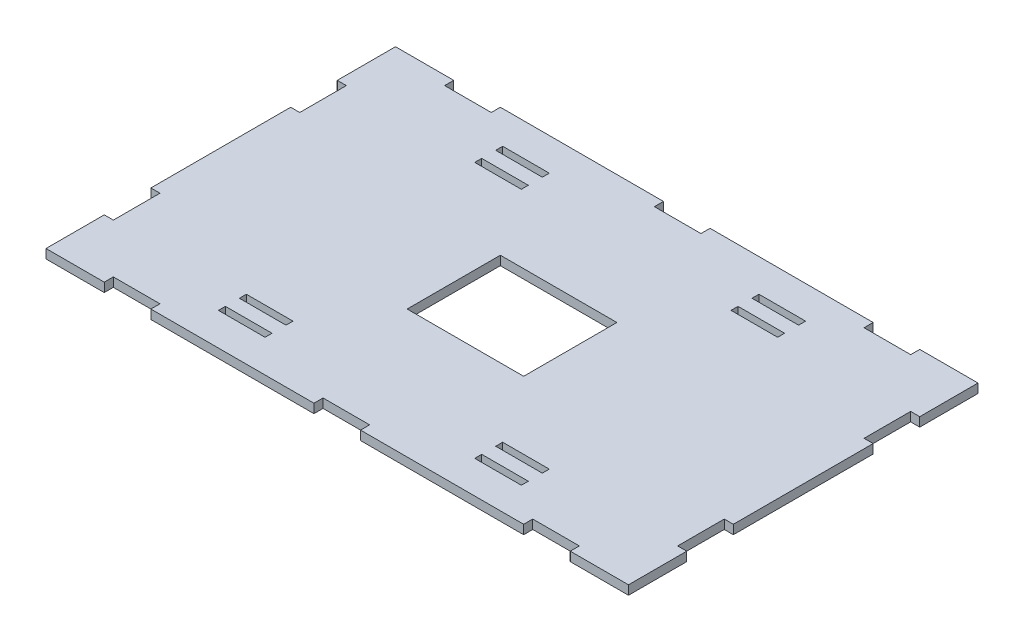
SolidWorks part; units mm, degrees
material "Very Low Density PE (SS)"
ref_plane "Front Plane" through (0, 0, 0) normal (0, 0, 1) x (1, 0, 0)
ref_plane "Top Plane" through (0, 0, 0) normal (0, 1, 0) x (1, 0, 0)
ref_plane "Right Plane" through (0, 0, 0) normal (1, 0, 0) x (0, 0, -1)
sketch "Sketch1" plane through (0, 0, 0) normal (0, 1, 0) x (1, 0, 0)
  line L0 (-125, 0) -> (125, 0) construction
  line L1 (-125, 75) -> (-100, 75)
  line L2 (-125, 75) -> (-125, 50)
  line L3 (-125, -75) -> (-100, -75)
  line L4 (125, 75) -> (125, 50)
  line L5 (0, 75) -> (0, -75) construction
  line L6 (-125, -55) -> (125, -55) construction
  line L11 (-65, -49) -> (-45, -49)
  line L12 (-65, -58) -> (-45, -58)
  line L25 (-65, -58) -> (-65, -61)
  line L26 (-25, 20) -> (25, 20)
  line L27 (-25, 20) -> (-25, -20)
  line L28 (-25, -20) -> (25, -20)
  line L29 (25, 20) -> (25, -20)
  line L30 (-25, 20) -> (25, -20) construction
  line L31 (-25, -20) -> (25, 20) construction
  line L32 (-65, -61) -> (-45, -61)
  line L33 (-45, -58) -> (-45, -61)
  line L34 (-45, -52) -> (-45, -49)
  line L35 (-65, -52) -> (-45, -52)
  line L36 (-65, -52) -> (-65, -49)
  line L37 (65, -61) -> (45, -61)
  line L38 (45, -58) -> (45, -61)
  line L39 (65, -58) -> (45, -58)
  line L40 (65, -58) -> (65, -61)
  line L41 (65, -52) -> (65, -49)
  line L42 (65, -52) -> (45, -52)
  line L43 (45, -52) -> (45, -49)
  line L44 (65, -49) -> (45, -49)
  line L45 (65, 52) -> (45, 52)
  line L46 (45, 52) -> (45, 49)
  line L47 (65, 49) -> (45, 49)
  line L48 (65, 52) -> (65, 49)
  line L49 (65, 58) -> (65, 61)
  line L50 (65, 58) -> (45, 58)
  line L51 (45, 58) -> (45, 61)
  line L52 (65, 61) -> (45, 61)
  line L53 (-65, 61) -> (-45, 61)
  line L54 (-45, 58) -> (-45, 61)
  line L55 (-65, 58) -> (-45, 58)
  line L56 (-65, 58) -> (-65, 61)
  line L57 (-65, 52) -> (-65, 49)
  line L58 (-65, 52) -> (-45, 52)
  line L59 (-45, 52) -> (-45, 49)
  line L60 (-65, 49) -> (-45, 49)
  line L61 (100, -71.1) -> (80, -71.1)
  line L63 (-100, -75) -> (-100, -71.1)
  line L64 (-100, -71.1) -> (-80, -71.1)
  line L65 (-80, -75) -> (-80, -71.1)
  line L66 (80, -75) -> (80, -71.1)
  line L68 (100, -75) -> (100, -71.1)
  line L69 (10, -75) -> (80, -75)
  line L70 (-10, -71.1) -> (10, -71.1)
  line L71 (-10, -71.1) -> (-10, -75)
  line L73 (10, -71.1) -> (10, -75)
  line L74 (-10, -71.1) -> (10, -75) construction
  line L75 (-10, -75) -> (10, -71.1) construction
  line L76 (-80, -75) -> (-10, -75)
  line L77 (100, -75) -> (125, -75)
  line L78 (100, 75) -> (100, 71.1)
  line L79 (80, 75) -> (80, 71.1)
  line L80 (100, 71.1) -> (80, 71.1)
  line L81 (10, 71.1) -> (10, 75)
  line L82 (-10, 71.1) -> (10, 71.1)
  line L83 (-10, 71.1) -> (-10, 75)
  line L84 (-80, 75) -> (-80, 71.1)
  line L85 (-100, 71.1) -> (-80, 71.1)
  line L86 (-100, 75) -> (-100, 71.1)
  line L87 (-10, 75) -> (0, 75) construction
  line L88 (10, 75) -> (80, 75)
  line L89 (0, 75) -> (10, 75) construction
  line L90 (-100, 75) -> (-80, 75) construction
  line L91 (-80, 75) -> (-10, 75)
  line L92 (80, 75) -> (100, 75) construction
  line L93 (100, 75) -> (125, 75)
  line L94 (125, -30) -> (121.1, -30)
  line L95 (125, 50) -> (121.1, 50)
  line L96 (125, 50) -> (125, 30) construction
  line L97 (125, 30) -> (121.1, 30)
  line L98 (121.1, 50) -> (121.1, 30)
  line L99 (121.1, -50) -> (121.1, -30)
  line L100 (125, -50) -> (121.1, -50)
  line L101 (125, -50) -> (125, -30) construction
  line L102 (125, 50) -> (125, 30) construction
  line L103 (125, 30) -> (125, -30)
  line L104 (125, -30) -> (125, -50) construction
  line L105 (125, -50) -> (125, -75)
  line L106 (-125, -30) -> (-121.1, -30)
  line L107 (-121.1, -50) -> (-121.1, -30)
  line L108 (-125, -50) -> (-121.1, -50)
  line L109 (-125, 30) -> (-121.1, 30)
  line L110 (-125, 50) -> (-121.1, 50)
  line L111 (-121.1, 50) -> (-121.1, 30)
  line L112 (-125, 50) -> (-125, 30) construction
  line L113 (-125, 30) -> (-125, -30)
  line L114 (-125, -30) -> (-125, -50) construction
  line L115 (-125, -50) -> (-125, -75)
  point P0 (0, 0)
  point P29 (0, 0)
  point P57 (0, -73.05)
  dimension "D2" = 150
  dimension "D3" = 3
  dimension "D4" = 20
  dimension "D5" = 25
  dimension "D6" = 20
  dimension "D7" = 40
  dimension "D8" = 50
  dimension "D9" = 3
  dimension "D10" = 45
  dimension "D11" = 20
  dimension "D12" = 3.9
  dimension "D13" = 20
  dimension "D15" = 25
  dimension "D16" = 20
  dimension "D17" = 3.9
  dimension "D18" = 250
extrude "Boss-Extrude1" add sketch "Sketch1" along normal blind 3.9
